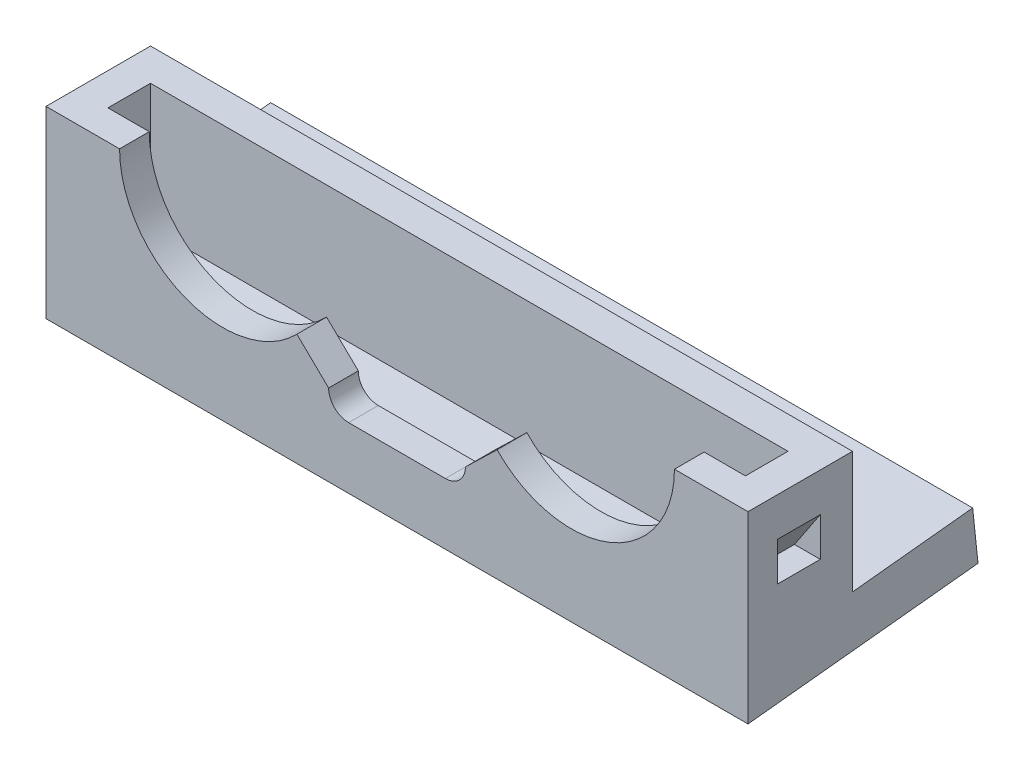
SolidWorks part; units mm, degrees
ref_plane "Front Plane" through (0, 0, 0) normal (0, 0, 1) x (1, 0, 0)
ref_plane "Top Plane" through (0, 0, 0) normal (0, 1, 0) x (1, 0, 0)
ref_plane "Right Plane" through (0, 0, 0) normal (1, 0, 0) x (0, 0, -1)
sketch "Sketch2" plane through (0, 0, 0) normal (0, 1, 0) x (1, 0, 0)
  line L1 (-27.2, -8) -> (27.2, -8)
  line L2 (-27.2, -8) -> (-27.2, 8)
  line L3 (-27.2, 8) -> (27.2, 8)
  line L4 (27.2, -8) -> (27.2, 8)
  line L5 (-27.2, -8) -> (27.2, 8) construction
  line L6 (-27.2, 8) -> (27.2, -8) construction
  point P0 (0, 0)
extrude "Boss-Extrude1" add sketch "Sketch2" along normal blind 4
sketch "Sketch3" plane through (27.2, 0, 0) normal (1, 0, 0) x (0, 0, -1)
  line L1 (-8, 0) -> (-10.3, 0)
  line L2 (-8, 0) -> (-8, 24)
  line L3 (-8, 24) -> (-10.3, 24)
  line L4 (-10.3, 0) -> (-10.3, 24)
extrude "Boss-Extrude2" add sketch "Sketch3" against normal blind 54.4
sketch "Sketch4" plane through (0, 4, 0) normal (0, 1, 0) x (1, 0, 0)
  line L0 (-27.2, 8) -> (-27.2, -8) construction
  line L1 (27.2, 8) -> (-27.2, 8) construction
  circle A0 centre (-13.5, 2.5) radius 2.3
  circle A1 centre (13.5, 2.5) radius 2.3
  dimension "D1" = 27
  dimension "D2" = 13.7
  dimension "D3" = 5.5
  dimension "D4" = 5.5
extrude "Cut-Extrude1" cut sketch "Sketch4" against normal blind 45
sketch "Sketch6" plane through (0, 0, 10.3) normal (0, 0, 1) x (1, 0, 0)
  line L0 (-3.75, 6.3) -> (3.75, 6.3) construction
  line L1 (-3.75, 7.85) -> (3.75, 7.85)
  line L2 (-3.75, 4.75) -> (3.75, 4.75)
  line L3 (-27.2, 0) -> (27.2, 0) construction
  arc A0 (-3.75, 7.85) -> (-3.75, 4.75) centre (-3.75, 6.3) ccw
  arc A1 (3.75, 4.75) -> (3.75, 7.85) centre (3.75, 6.3) ccw
  point P2 (0, 6.3)
  dimension "D3" = 1.55
  dimension "D1" = 4.75
  dimension "D2" = 7.5
extrude "Cut-Extrude3" cut sketch "Sketch6" against normal blind 10
sketch "Sketch5" plane through (0, 0, 10.3) normal (0, 0, 1) x (1, 0, 0)
  line L0 (-27.2, 0) -> (27.2, 0) construction
  line L1 (-27.2, 24) -> (-27.2, 0) construction
  circle A0 centre (-13.5, 14.25) radius 8
  circle A1 centre (13.5, 14.25) radius 8
  dimension "D1" = 14.25
  dimension "D2" = 27
  dimension "D3" = 14.25
  dimension "D4" = 13.7
extrude "Cut-Extrude2" cut sketch "Sketch5" against normal blind 10
sketch "Sketch7" plane through (0, 0, 10.3) normal (0, 0, 1) x (1, 0, 0)
  line L0 (-35.2427, 14.25) -> (-13.5, 14.25)
  line L1 (0, 6.5) -> (-5.3, 6.3)
  line L2 (-5.3, 6.3) -> (-13.5, 14.25)
  line L3 (0, 6.5) -> (5.3, 6.3)
  line L4 (13.5, 14.25) -> (21.5, 14.25)
  line L5 (-35.2427, 14.25) -> (-35.2427, 27.8876)
  line L6 (-35.2427, 27.8876) -> (36.0064, 27.8876)
  line L7 (5.3, 6.3) -> (13.5, 14.25)
  line L8 (36.0064, 14.25) -> (36.0064, 27.8876)
  line L9 (21.5, 14.25) -> (36.0064, 14.25)
  arc A0 (-3.75, 7.85) -> (-3.75, 4.75) centre (-3.75, 6.3) ccw construction
  arc A1 (3.75, 4.75) -> (3.75, 7.85) centre (3.75, 6.3) ccw construction
  circle A2 centre (13.5, 14.25) radius 8 construction
  point P10 (0, 6.5)
extrude "Cut-Extrude4" cut sketch "Sketch7" against normal blind 10
sketch "Sketch8" plane through (27.2, 0, 0) normal (1, 0, 0) x (0, 0, -1)
  line L0 (-8, 4) -> (8, 4) construction
  line L2 (-4.7, 14.25) -> (-2.2, 14.25)
  line L3 (-4.7, 14.25) -> (-4.7, 4)
  line L4 (-4.7, 4) -> (-2.2, 4)
  line L8 (-2.2, 14.25) -> (-2.2, 4)
  line L9 (-4.7, 14.25) -> (-2.2, 4) construction
  line L10 (-4.7, 4) -> (-2.2, 14.25) construction
  line L11 (-8, 4) -> (-8, 14.25) construction
  point P0 (-3.45, 9.125)
  dimension "D1" = 0
  dimension "D2" = 3.3
  dimension "D3" = 2.5
extrude "Boss-Extrude3" add sketch "Sketch8" against normal blind 54.4
sketch "Sketch9" plane through (0, 4, 0) normal (0, 1, 0) x (1, 0, 0)
  line L1 (-27.2, -4.7) -> (27.2, -4.7) construction
  line L2 (-27.2, -4.7) -> (-24.7, -4.7)
  line L3 (-27.2, -4.7) -> (-27.2, -8)
  line L4 (-27.2, -8) -> (-24.7, -8)
  line L5 (-24.7, -4.7) -> (-24.7, -8)
  line L6 (-27.2, -4.7) -> (-24.7, -8) construction
  line L7 (-27.2, -8) -> (-24.7, -4.7) construction
  line L8 (-27.2, -8) -> (27.2, -8) construction
  line L9 (-27.2, -4.7) -> (-27.2, -8) construction
  line L10 (-27.2, -4.7) -> (27.2, -4.7) construction
  line L11 (27.2, -4.7) -> (24.7, -4.7)
  line L12 (27.2, -4.7) -> (27.2, -8)
  line L13 (27.2, -8) -> (24.7, -8)
  line L14 (24.7, -4.7) -> (24.7, -8)
  line L15 (27.2, -4.7) -> (24.7, -8) construction
  line L16 (27.2, -8) -> (24.7, -4.7) construction
  line L17 (27.2, -8) -> (27.2, -4.7) construction
  point P0 (-25.95, -6.35)
  point P13 (25.95, -6.35)
  dimension "D1" = 0
  dimension "D2" = 0
  dimension "D3" = 0
  dimension "D4" = 2.5
  dimension "D5" = 0
  dimension "D6" = 0
  dimension "D7" = 0
  dimension "D8" = 2.5
extrude "Boss-Extrude4" add sketch "Sketch9" along normal blind 10.25
sketch "Sketch10" plane through (0, 0, 4.7) normal (0, 0, 1) x (1, 0, 0)
  line L0 (-27.2, 8.25) -> (-25.2, 8.25)
  line L1 (27.2, 14.25) -> (27.2, 0) construction
  line L3 (27.2, 11.25) -> (27.2, 8.25)
  line L5 (-27.2, 11.25) -> (-27.2, 8.25)
  line L6 (27.2, 8.25) -> (25.2, 8.25)
  line L7 (25.2, 8.25) -> (27.2, 11.25)
  line L8 (-25.2, 8.25) -> (-27.2, 11.25)
extrude "Cut-Extrude5" cut sketch "Sketch10" along normal blind 3.3
sketch "Sketch11" plane through (0, 4, 0) normal (0, 1, 0) x (1, 0, 0)
  line L1 (-27.2, 8) -> (27.2, 8)
  line L2 (-27.2, 8) -> (-27.2, -2.2)
  line L3 (-27.2, -2.2) -> (27.2, -2.2)
  line L4 (27.2, 8) -> (27.2, -2.2)
extrude "Cut-Extrude6" cut sketch "Sketch11" against normal blind 10
sketch "Sketch12" plane through (-27.2, 0, 0) normal (-1, 0, 0) x (0, 0, 1)
  line L0 (10.3, 0) -> (-7.5224, 1.8732)
  line L1 (-7.5224, 1.8732) -> (-7.1103, 5.7939)
  line L2 (-7.1103, 5.7939) -> (10.3, 3.964)
  line L4 (10.3, 14.25) -> (10.3, 0) construction
  line L5 (10.3, 3.964) -> (10.3, 0)
extrude "Boss-Extrude5" add sketch "Sketch12" against normal blind 54.4
sketch "Sketch13" plane through (27.2, 0, 0) normal (1, 0, 0) x (0, 0, -1)
  line L0 (-2.2, 0.8513) -> (-10.3, 0)
  line L1 (-10.3, 0) -> (-2.2, 0)
  line L2 (-2.2, 0) -> (-2.2, 0.8513)
extrude "Cut-Extrude7" cut sketch "Sketch13" against normal blind 54.4
sketch "Sketch14" plane through (0, 4.9915, 0.5246) normal (0, 0.9945, 0.1045) x (1, 0, 0)
  circle A0 centre (-13.5, 2.9044) radius 2.3
  circle A1 centre (13.5, 2.9044) radius 2.3
extrude "Cut-Extrude8" cut sketch "Sketch14" against normal blind 54.4
